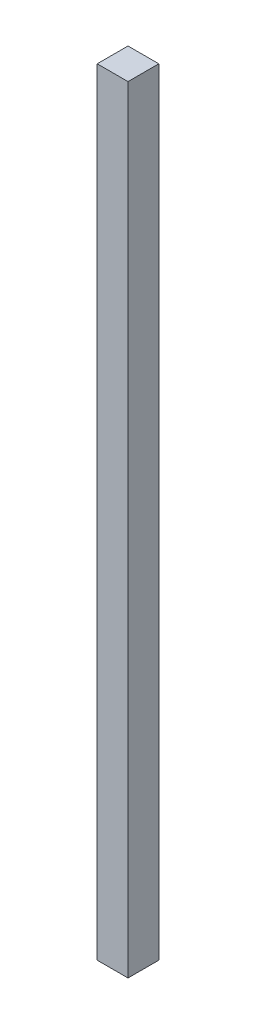
SolidWorks part; units mm, degrees
ref_plane "Спереди" through (0, 0, 0) normal (0, 0, 1) x (1, 0, 0)
ref_plane "Сверху" through (0, 0, 0) normal (0, 1, 0) x (1, 0, 0)
ref_plane "Справа" through (0, 0, 0) normal (1, 0, 0) x (0, 0, -1)
sketch "Эскиз1" plane through (0, 0, 0) normal (0, 1, 0) x (1, 0, 0)
  line L1 (-2.5, 2.5) -> (2.5, 2.5)
  line L2 (-2.5, 2.5) -> (-2.5, -2.5)
  line L3 (-2.5, -2.5) -> (2.5, -2.5)
  line L4 (2.5, 2.5) -> (2.5, -2.5)
  line L5 (-2.5, 2.5) -> (2.5, -2.5) construction
  line L6 (-2.5, -2.5) -> (2.5, 2.5) construction
  point P0 (0, 0)
extrude "Бобышка-Вытянуть1" add sketch "Эскиз1" along normal blind 126
sketch "Эскиз2" plane through (2.5, 0, 0) normal (1, 0, 0) x (0, 0, -1)
  line L0 (0, 126) -> (0, 0)
  line L1 (-2.5, 126) -> (2.5, 126) construction
  line L2 (-2.5, 0) -> (2.5, 0) construction
